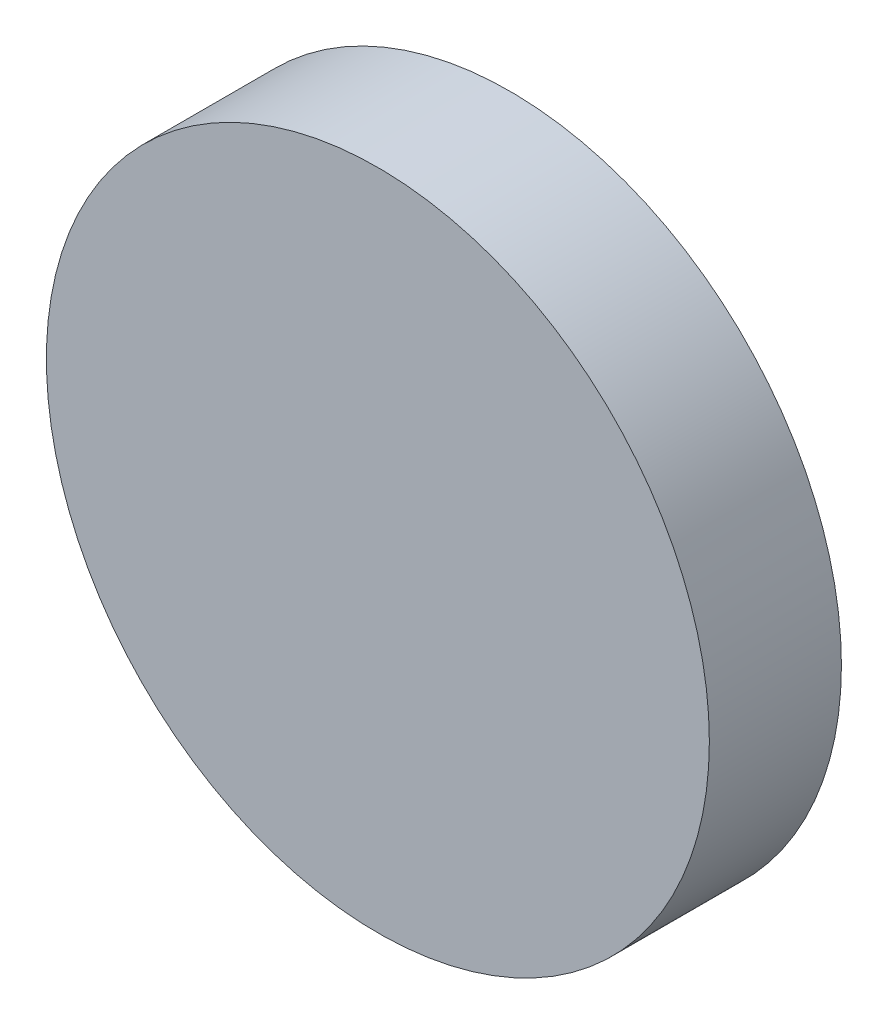
SolidWorks part; units mm, degrees
ref_plane "Front Plane" through (0, 0, 0) normal (0, 0, 1) x (1, 0, 0)
ref_plane "Top Plane" through (0, 0, 0) normal (0, 1, 0) x (1, 0, 0)
ref_plane "Right Plane" through (0, 0, 0) normal (1, 0, 0) x (0, 0, -1)
sketch "Sketch1" plane through (0, 0, 0) normal (0, 0, 1) x (1, 0, 0)
  circle A1 centre (-5.5808, 1.5115) radius 31.8767
extrude "Boss-Extrude1" add sketch "Sketch1" along normal blind 12.7
